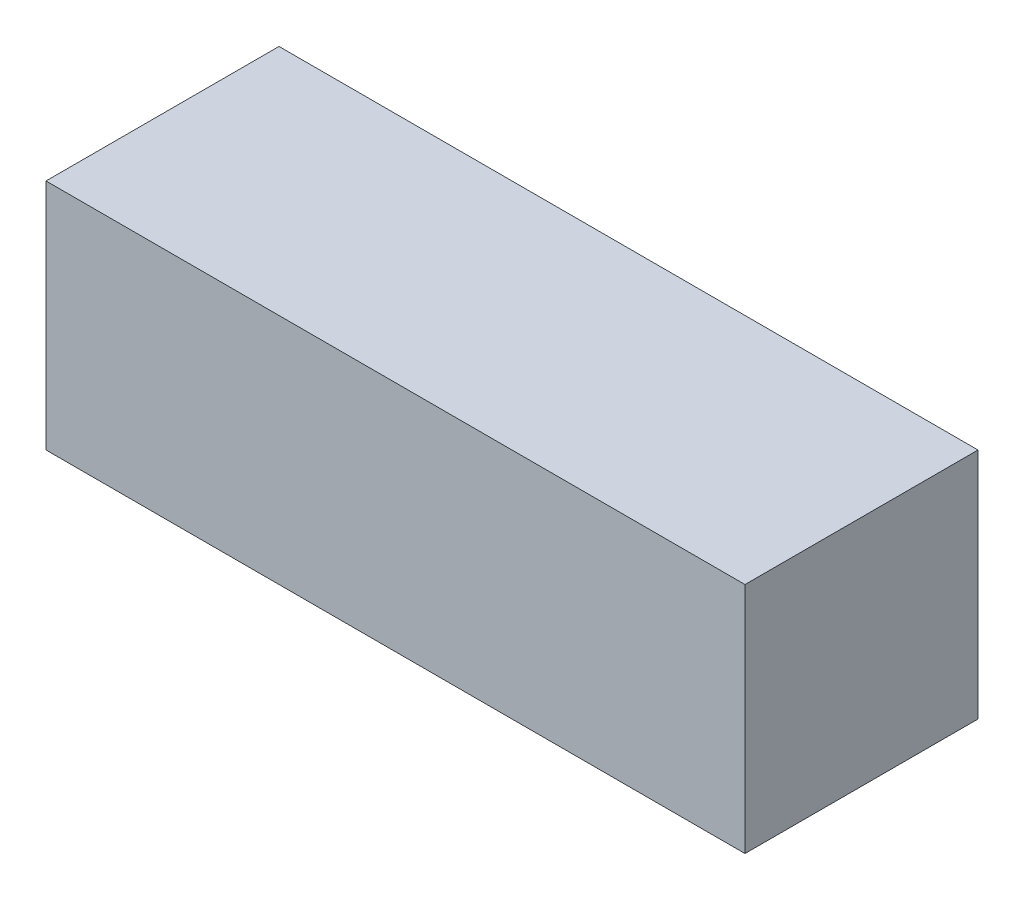
SolidWorks part; units mm, degrees
ref_plane "Front Plane" through (0, 0, 0) normal (0, 0, 1) x (1, 0, 0)
ref_plane "Top Plane" through (0, 0, 0) normal (0, 1, 0) x (1, 0, 0)
ref_plane "Right Plane" through (0, 0, 0) normal (1, 0, 0) x (0, 0, -1)
sketch "Sketch1" plane through (0, 0, 0) normal (1, 0, 0) x (0, 0, -1)
  line L1 (-41.1471, 67.8245) -> (58.8529, 67.8245)
  line L2 (-41.1471, 67.8245) -> (-41.1471, -32.1755)
  line L3 (-41.1471, -32.1755) -> (58.8529, -32.1755)
  line L4 (58.8529, 67.8245) -> (58.8529, -32.1755)
  dimension "D1" = 100
  dimension "D2" = 100
extrude "Boss-Extrude1" add sketch "Sketch1" along normal blind 300
